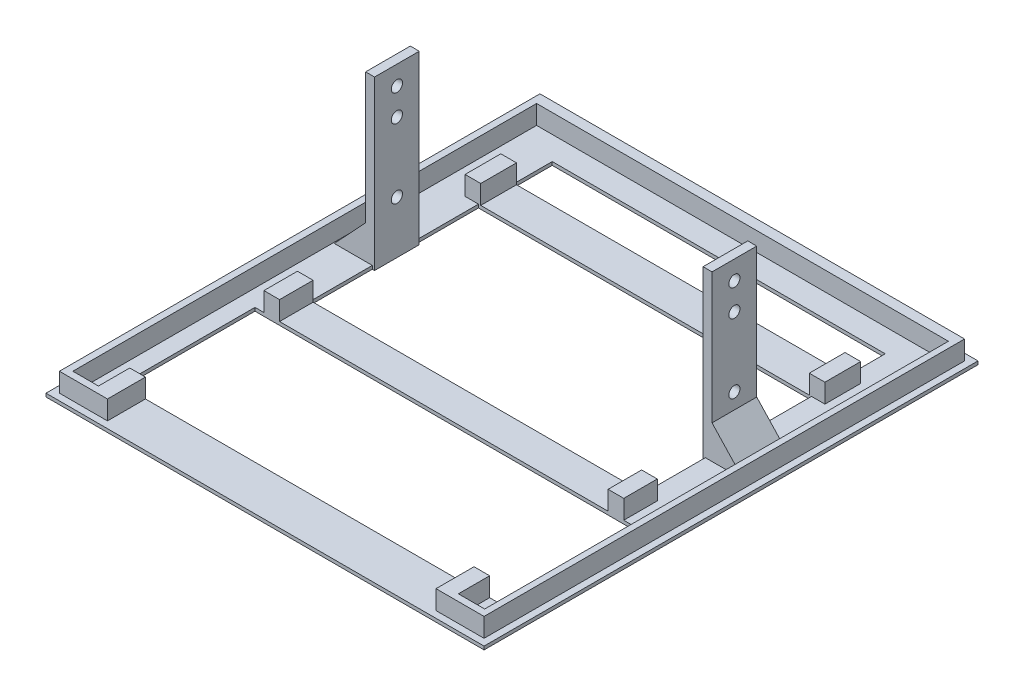
SolidWorks part; units mm, degrees
ref_plane "前视基准面" through (0, 0, 0) normal (0, 0, 1) x (1, 0, 0)
ref_plane "上视基准面" through (0, 0, 0) normal (0, 1, 0) x (1, 0, 0)
ref_plane "右视基准面" through (0, 0, 0) normal (1, 0, 0) x (0, 0, -1)
sketch "草图1" plane through (0, 0, 0) normal (0, 1, 0) x (1, 0, 0)
  line L1 (0, 0) -> (196, 0)
  line L2 (0, 0) -> (0, 221)
  line L3 (0, 221) -> (196, 221)
  line L4 (196, 0) -> (196, 221)
  line L6 (13.5, 20) -> (13.5, 80)
  line L7 (13.5, 80) -> (182.5, 80)
  line L8 (182.5, 80) -> (182.5, 20)
  line L9 (182.5, 20) -> (13.5, 20)
  line L10 (23.5, 95) -> (23.5, 170)
  line L11 (23.5, 170) -> (172.5, 170)
  line L12 (172.5, 170) -> (172.5, 95)
  line L13 (172.5, 95) -> (23.5, 95)
  line L15 (23.5, 186) -> (23.5, 203)
  line L16 (23.5, 203) -> (172.5, 203)
  line L17 (172.5, 203) -> (172.5, 186)
  line L18 (172.5, 186) -> (23.5, 186)
  line L20 (27, 218) -> (186, 218)
  line L21 (186, 218) -> (186, 214.5)
  line L22 (186, 214.5) -> (27, 214.5)
  line L23 (27, 214.5) -> (27, 218)
extrude "凸台-拉伸1" add sketch "草图1" along normal blind 1.5
ref_plane "基准面1" through (0, 1.5, 0) normal (0, 1, 0) x (1, 0, 0)
sketch "草图3" plane through (0, 1.5, 0) normal (0, 1, 0) x (1, 0, 0)
  line L0 (171.5, 20) -> (178.5, 20)
  line L1 (24.5, 3) -> (3, 3)
  line L2 (178.5, 20) -> (178.5, 6)
  line L3 (178.5, 80) -> (178.5, 95)
  line L4 (13.5, 20) -> (182.5, 20) construction
  line L5 (6.0023, 213.5) -> (6.0023, 6)
  line L6 (24.5, 20) -> (17.4739, 20)
  line L7 (17.4739, 20) -> (17.4739, 6)
  line L8 (6.0023, 6) -> (17.4739, 6)
  line L9 (178.5, 6) -> (190.2723, 6)
  line L11 (182.5, 80) -> (13.5, 80) construction
  line L12 (178.5, 95) -> (171.5, 95)
  line L13 (23.5, 95) -> (172.5, 95) construction
  line L14 (171.5, 95) -> (171.5, 80)
  line L15 (171.5, 80) -> (178.5, 80)
  line L16 (24.5, 80) -> (24.5, 95)
  line L17 (24.5, 95) -> (17.5, 95)
  line L18 (17.5, 95) -> (17.5, 80)
  line L19 (17.5, 80) -> (24.5, 80)
  line L20 (24.5, 170) -> (24.5, 186)
  line L21 (172.5, 170) -> (23.5, 170) construction
  line L22 (23.5, 186) -> (172.5, 186) construction
  line L23 (24.5, 186) -> (17.5, 186)
  line L24 (17.5, 186) -> (17.5, 170)
  line L25 (17.5, 170) -> (23.5, 170)
  line L26 (178.5, 170) -> (178.5, 186)
  line L27 (178.5, 186) -> (171.5, 186)
  line L28 (171.5, 186) -> (171.5, 170)
  line L29 (171.5, 170) -> (178.5, 170)
  line L30 (171.5, 20) -> (171.5, 6)
  line L32 (24.5, 3) -> (24.5, 6.5294)
  line L33 (3, 3) -> (3, 218)
  line L34 (3, 218) -> (193, 218)
  line L35 (193, 218) -> (193, 3)
  line L36 (193, 3) -> (171.5, 3)
  line L37 (171.5, 3) -> (171.5, 6)
  line L38 (190.2723, 6) -> (190.2723, 213.5)
  line L39 (190.2723, 213.5) -> (6.0023, 213.5)
  line L40 (24.5, 6) -> (24.5, 20)
ref_plane "基准面3" through (0, 0, 0) normal (0, 1, 0) x (1, 0, 0)
sketch "草图5" plane through (0, 0, 0) normal (0, 1, 0) x (1, 0, 0)
  line L0 (3, 218) -> (193, 218)
  line L1 (193, 218) -> (193, 3)
  line L2 (193, 3) -> (171.5, 3)
  line L3 (171.5, 3) -> (171.5, 20)
  line L4 (171.5, 20) -> (178.5, 20)
  line L5 (178.5, 20) -> (178.5, 6)
  line L6 (178.5, 6) -> (190.2723, 6)
  line L7 (190.2723, 6) -> (190.2723, 213.5)
  line L8 (190.2723, 213.5) -> (6.0023, 213.5)
  line L9 (6.0023, 213.5) -> (6.0023, 6)
  line L10 (6.0023, 6) -> (17.4739, 6)
  line L11 (17.4739, 6) -> (17.4739, 20)
  line L12 (17.4739, 20) -> (24.5, 20)
  line L13 (24.5, 20) -> (24.5, 3)
  line L14 (24.5, 3) -> (3, 3)
  line L15 (3, 3) -> (3, 218)
  line L16 (17.5, 186) -> (24.5, 186)
  line L17 (24.5, 186) -> (24.5, 170)
  line L18 (24.5, 170) -> (17.5, 170)
  line L19 (17.5, 170) -> (17.5, 186)
  line L21 (178.5, 186) -> (178.5, 170)
  line L22 (178.5, 170) -> (171.5, 170)
  line L23 (171.5, 170) -> (171.5, 186)
  line L24 (171.5, 186) -> (178.5, 186)
  line L25 (171.5, 95) -> (178.5, 95)
  line L26 (178.5, 95) -> (178.5, 80)
  line L27 (178.5, 80) -> (171.5, 80)
  line L28 (171.5, 80) -> (171.5, 95)
  line L29 (17.5, 95) -> (24.5, 95)
  line L30 (24.5, 95) -> (24.5, 80)
  line L31 (24.5, 80) -> (17.5, 80)
  line L32 (17.5, 80) -> (17.5, 95)
extrude "凸台-拉伸9" add sketch "草图5" along normal blind 10
ref_plane "基准面4" through (0, 0, 0) normal (0, 1, 0) x (1, 0, 0)
sketch "草图6" plane through (0, 0, 0) normal (0, 1, 0) x (1, 0, 0)
  line L0 (27, 217.5863) -> (27, 218)
  line L3 (3, 218) -> (193, 218) construction
  line L4 (27, 218) -> (186, 218)
  line L5 (186, 218) -> (186, 215)
  line L6 (186, 215) -> (27, 215)
  line L7 (27, 215) -> (27, 217.5863)
extrude "切除-拉伸2" cut sketch "草图6" along normal blind 1.4
ref_plane "基准面5" through (0, 0, 0) normal (0, 1, 0) x (1, 0, 0)
sketch "草图7" plane through (0, 0, 0) normal (0, 1, 0) x (1, 0, 0)
  line L0 (175.5, 132.5) -> (175.5, 142.5)
  line L2 (175.5, 142.5) -> (171.5, 142.5)
  line L3 (171.5, 142.5) -> (171.5, 122.5)
  line L4 (171.5, 122.5) -> (175.5, 122.5)
  line L5 (175.5, 122.5) -> (175.5, 132.5)
  line L6 (24.5, 142.5) -> (20.5, 142.5)
  line L7 (20.5, 142.5) -> (20.5, 122.5)
  line L9 (24.5, 142.5) -> (24.5, 122.5)
  line L10 (20.5, 122.5) -> (24.5, 122.5)
extrude "凸台-拉伸10" add sketch "草图7" along normal blind 75
ref_plane "基准面6" through (175.5, 0, 0) normal (1, 0, 0) x (0, 0, -1)
sketch "草图8" plane through (175.5, 0, 0) normal (1, 0, 0) x (0, 0, -1)
  circle A0 centre (132.5, 66.5) radius 2.5
  circle A1 centre (132.5, 54.5) radius 2.5
  circle A2 centre (132.5, 23.5) radius 2.5
extrude "切除-拉伸3" cut sketch "草图8" against normal blind 185
ref_plane "基准面7" through (0, 0, -142.5) normal (0, 0, -1) x (-1, 0, 0)
sketch "草图10" plane through (0, 0, -142.5) normal (0, 0, -1) x (-1, 0, 0)
  line L0 (-189.5, 1.5) -> (-175.5, 1.5)
  line L1 (-20.5, 1.5) -> (-6.5, 1.5)
  line L4 (-175.5, 1.5) -> (-175.5, 16.5)
  line L5 (-175.5, 16.5) -> (-189.5, 1.5)
  line L8 (-20.5, 1.5) -> (-20.5, 16.5)
  line L9 (-20.5, 75) -> (-20.5, 1.5) construction
  line L10 (-20.5, 16.5) -> (-6.5, 1.5)
extrude "凸台-拉伸11" add sketch "草图10" against normal blind 20
